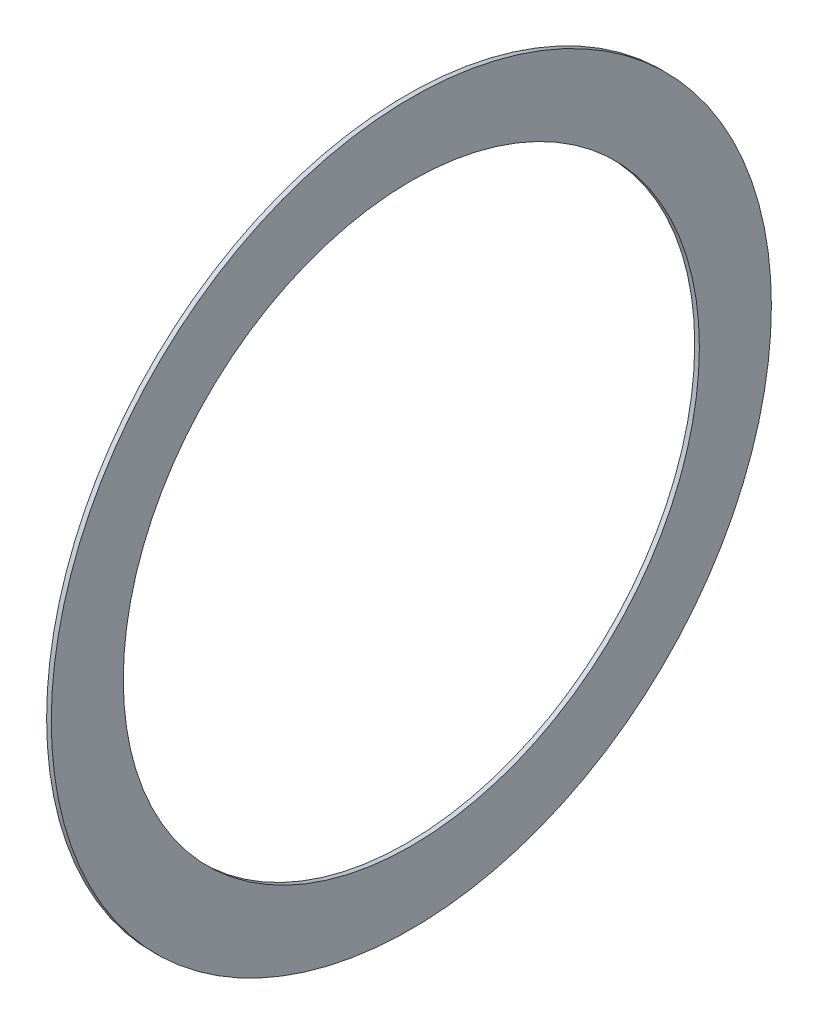
SolidWorks part; units mm, degrees
ref_plane "Front Plane" through (0, 0, 0) normal (0, 0, 1) x (1, 0, 0)
ref_plane "Top Plane" through (0, 0, 0) normal (0, 1, 0) x (1, 0, 0)
ref_plane "Right Plane" through (0, 0, 0) normal (1, 0, 0) x (0, 0, -1)
sketch "Sketch1" plane through (0, 0, 0) normal (1, 0, 0) x (0, 0, -1)
  circle A0 centre (0, 0) radius 124
  circle A1 centre (0, 0) radius 155
  dimension "D1" = 310
  dimension "D2" = 248
extrude "Boss-Extrude1" add sketch "Sketch1" along normal blind 2
